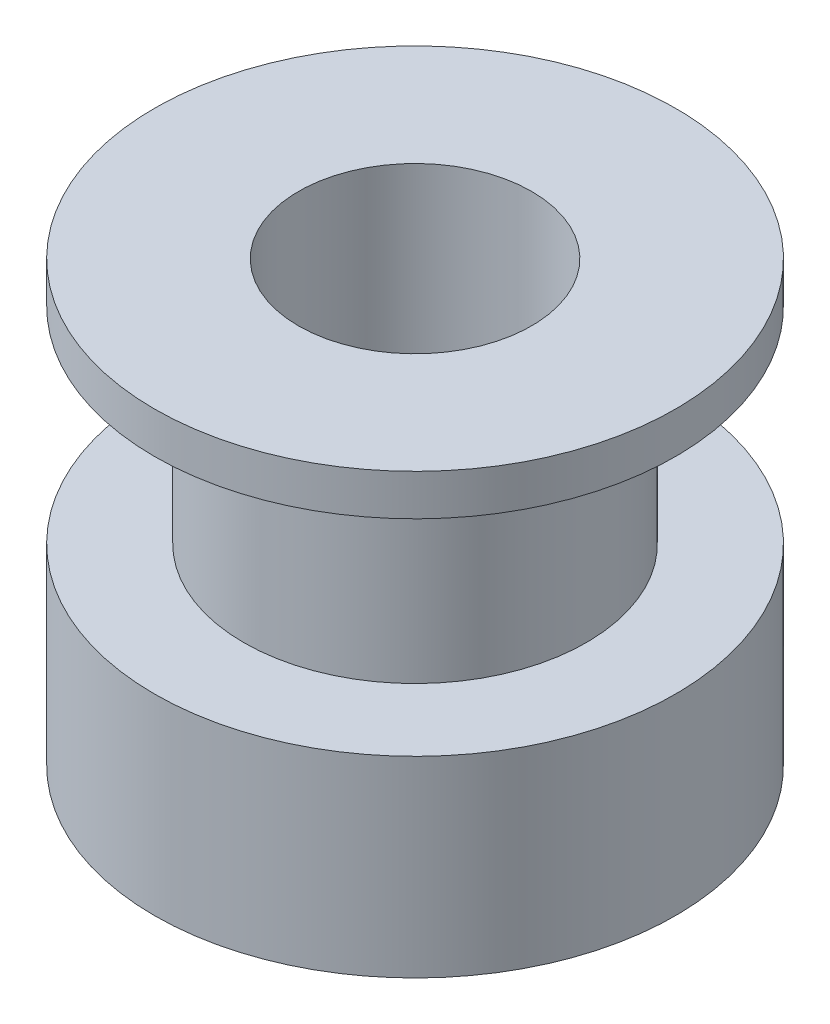
SolidWorks part; units mm, degrees
ref_plane "Front Plane" through (0, 0, 0) normal (0, 0, 1) x (1, 0, 0)
ref_plane "Top Plane" through (0, 0, 0) normal (0, 1, 0) x (1, 0, 0)
ref_plane "Right Plane" through (0, 0, 0) normal (1, 0, 0) x (0, 0, -1)
sketch "Sketch1" plane through (0, 0, 0) normal (0, 1, 0) x (1, 0, 0)
  circle A0 centre (0, 0) radius 9.5
  dimension "D1" = 19
extrude "Boss-Extrude1" add sketch "Sketch1" along normal blind 7
sketch "Sketch2" plane through (0, 7, 0) normal (0, 1, 0) x (1, 0, 0)
  circle A0 centre (0, 0) radius 6.25
  dimension "D1" = 12.5
extrude "Boss-Extrude2" add sketch "Sketch2" along normal blind 7.5
sketch "Sketch3" plane through (0, 14.5, 0) normal (0, 1, 0) x (1, 0, 0)
  circle A0 centre (0, 0) radius 9.5
  dimension "D1" = 19
extrude "Boss-Extrude3" add sketch "Sketch3" along normal blind 1.5
sketch "Sketch4" plane through (0, 16, 0) normal (0, 1, 0) x (1, 0, 0)
  circle A0 centre (0, 0) radius 4.25
  dimension "D1" = 8.5
extrude "Cut-Extrude1" cut sketch "Sketch4" against normal through all
